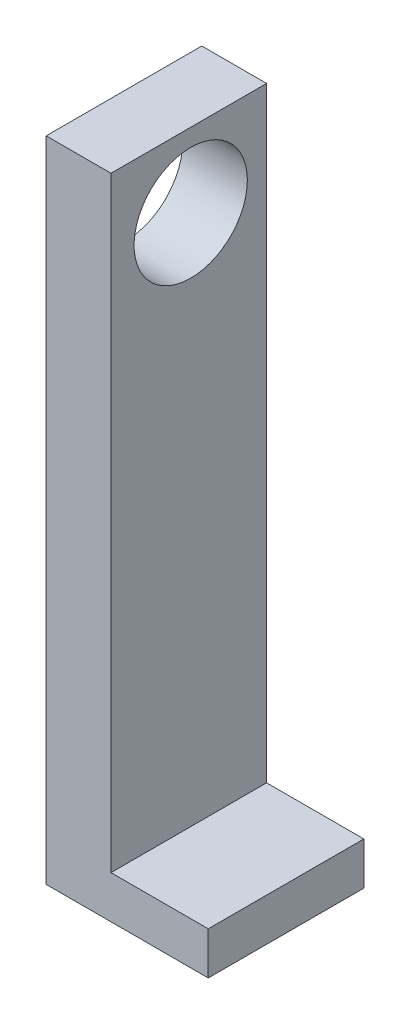
SolidWorks part; units mm, degrees
ref_plane "Front Plane" through (0, 0, 0) normal (0, 0, 1) x (1, 0, 0)
ref_plane "Top Plane" through (0, 0, 0) normal (0, 1, 0) x (1, 0, 0)
ref_plane "Right Plane" through (0, 0, 0) normal (1, 0, 0) x (0, 0, -1)
sketch "Sketch1" plane through (0, 0, 0) normal (1, 0, 0) x (0, 0, -1)
  line L1 (-12.2981, -88.5735) -> (11.7019, -88.5735)
  line L2 (-12.2981, -88.5735) -> (-12.2981, 11.4265)
  line L3 (-12.2981, 11.4265) -> (11.7019, 11.4265)
  line L4 (11.7019, -88.5735) -> (11.7019, 11.4265)
  circle A0 centre (0, 0) radius 8.735
extrude "Boss-Extrude1" add sketch "Sketch1" along normal blind 10
sketch "Sketch2" plane through (10, 0, 0) normal (1, 0, 0) x (0, 0, -1)
  line L0 (11.7019, -88.5735) -> (11.7019, 11.4265) construction
  line L1 (-12.2981, -88.5735) -> (11.7019, -88.5735)
  line L2 (-12.2981, -88.5735) -> (-12.2981, -82)
  line L3 (-12.2981, -82) -> (11.7019, -82)
  line L4 (11.7019, -88.5735) -> (11.7019, -82)
extrude "Boss-Extrude2" add sketch "Sketch2" along normal blind 15
